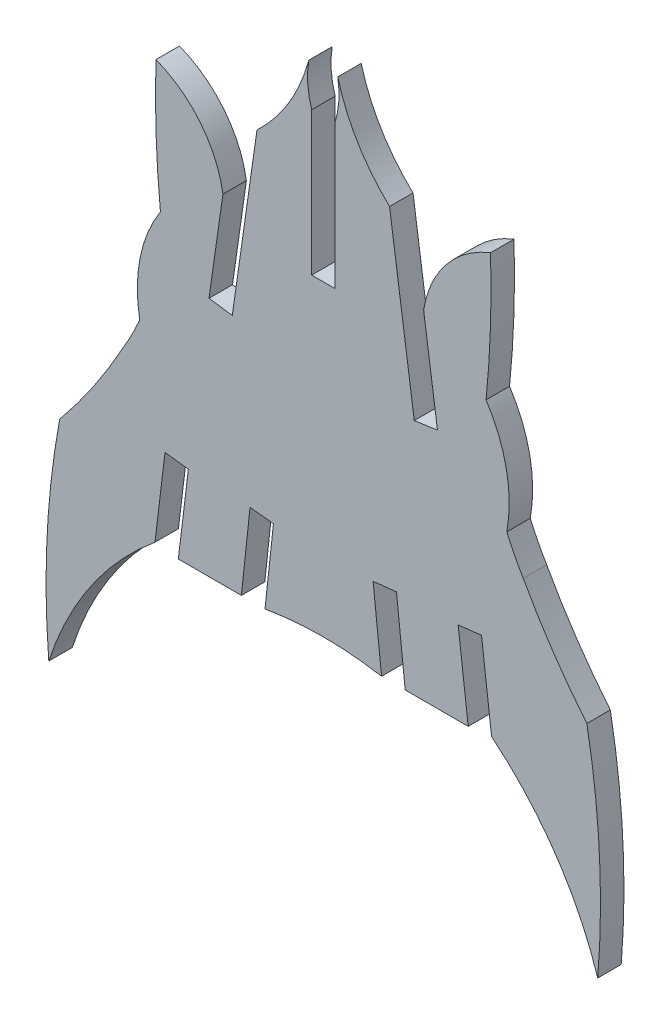
SolidWorks part; units mm, degrees
ref_plane "Front Plane" through (0, 0, 0) normal (0, 0, 1) x (1, 0, 0)
ref_plane "Top Plane" through (0, 0, 0) normal (0, 1, 0) x (1, 0, 0)
ref_plane "Right Plane" through (0, 0, 0) normal (1, 0, 0) x (0, 0, -1)
sketch "Sketch1" plane through (0, 0, 0) normal (0, 0, 1) x (1, 0, 0)
  line L0 (-3.7836, -13.3571) -> (-3.2352, -8.2874)
  line L1 (-3.2352, -8.2874) -> (-4.7552, -8.1225)
  line L2 (-4.7552, -8.1225) -> (-5.3175, -13.3591)
  line L3 (-5.3175, -13.3591) -> (-9.4106, -13.3581)
  line L4 (-9.4106, -13.3581) -> (-8.7589, -7.9834)
  line L5 (-8.7589, -7.9834) -> (-10.2749, -7.8006)
  line L6 (-10.2749, -7.8006) -> (-10.9267, -13.1743)
  line L7 (-6.5153, 8.606) -> (-7.4157, 2.3001)
  line L8 (-7.4157, 2.3001) -> (-5.9076, 2.0855)
  line L9 (-5.9076, 2.0855) -> (-4.3041, 13.3217)
  line L10 (-0.7514, 16.2327) -> (-0.7534, 6.9337)
  line L11 (-0.7534, 6.9337) -> (0.7745, 6.9337)
  line L12 (3.7836, -13.3571) -> (3.2352, -8.2874)
  line L13 (3.2352, -8.2874) -> (4.7552, -8.1225)
  line L14 (4.7552, -8.1225) -> (5.3175, -13.3591)
  line L15 (5.3175, -13.3591) -> (9.4106, -13.3581)
  line L16 (9.4106, -13.3581) -> (8.7589, -7.9834)
  line L17 (8.7589, -7.9834) -> (10.2749, -7.8006)
  line L18 (10.2749, -7.8006) -> (10.9267, -13.1743)
  line L19 (6.5153, 8.606) -> (7.4157, 2.3001)
  line L20 (7.4157, 2.3001) -> (5.9076, 2.0855)
  line L21 (5.9076, 2.0855) -> (4.3041, 13.3217)
  line L22 (0.7514, 16.2327) -> (0.7534, 6.9337)
  line L23 (0.7534, 6.9337) -> (-0.7745, 6.9337)
  line L24 (0, -13.0283) -> (0, -29.9007) construction
  arc A0 (-12.9796, -3.242) -> (-11.9169, -1.166) centre (-27.3388, 5.4189) ccw
  arc A1 (-4.3041, 13.3217) -> (-0.94, 18.9267) centre (-12.4314, 22.0118) ccw
  arc A2 (-0.94, 18.9267) -> (-0.7514, 16.2327) centre (4.6885, 17.9672) ccw
  arc A3 (-6.5153, 8.606) -> (-10.8612, 14) centre (-13.4008, 7.5062) ccw
  arc A4 (-10.8612, 14) -> (-10.5705, 5.5818) centre (52.783, 11.9833) ccw
  arc A5 (-17.1131, -9.3439) -> (-12.9796, -3.242) centre (-47.7944, 15.8907) ccw
  arc A6 (17.8203, -23.3018) -> (17.1131, -9.3439) centre (-34.5935, -18.9605) ccw
  arc A7 (-10.5705, 5.5818) -> (-11.9169, -1.166) centre (-2.8067, 0.5246) ccw
  arc A8 (11.9169, -1.166) -> (12.9796, -3.242) centre (27.3388, 5.4189) ccw
  arc A9 (0.94, 18.9267) -> (4.3041, 13.3217) centre (12.4314, 22.0118) ccw
  arc A10 (0.7514, 16.2327) -> (0.94, 18.9267) centre (-4.6885, 17.9672) ccw
  arc A11 (10.8612, 14) -> (6.5153, 8.606) centre (13.4008, 7.5062) ccw
  arc A12 (10.5705, 5.5818) -> (10.8612, 14) centre (-52.783, 11.9833) ccw
  arc A13 (12.9796, -3.242) -> (17.1131, -9.3439) centre (47.7944, 15.8907) ccw
  arc A15 (11.9169, -1.166) -> (10.5705, 5.5818) centre (2.8067, 0.5246) ccw
  arc A16 (-10.9267, -13.1743) -> (-17.8203, -23.3018) centre (2.868, -29.974) ccw
  arc A17 (-17.8203, -23.3018) -> (-17.1131, -9.3439) centre (34.5935, -18.9605) cw
  arc A18 (3.7836, -13.3571) -> (-3.7836, -13.3571) centre (0, -34.9644) ccw
  arc A19 (10.9267, -13.1743) -> (17.8203, -23.3018) centre (-2.868, -29.974) cw
extrude "Boss-Extrude1" add sketch "Sketch1" along normal blind 1.524
